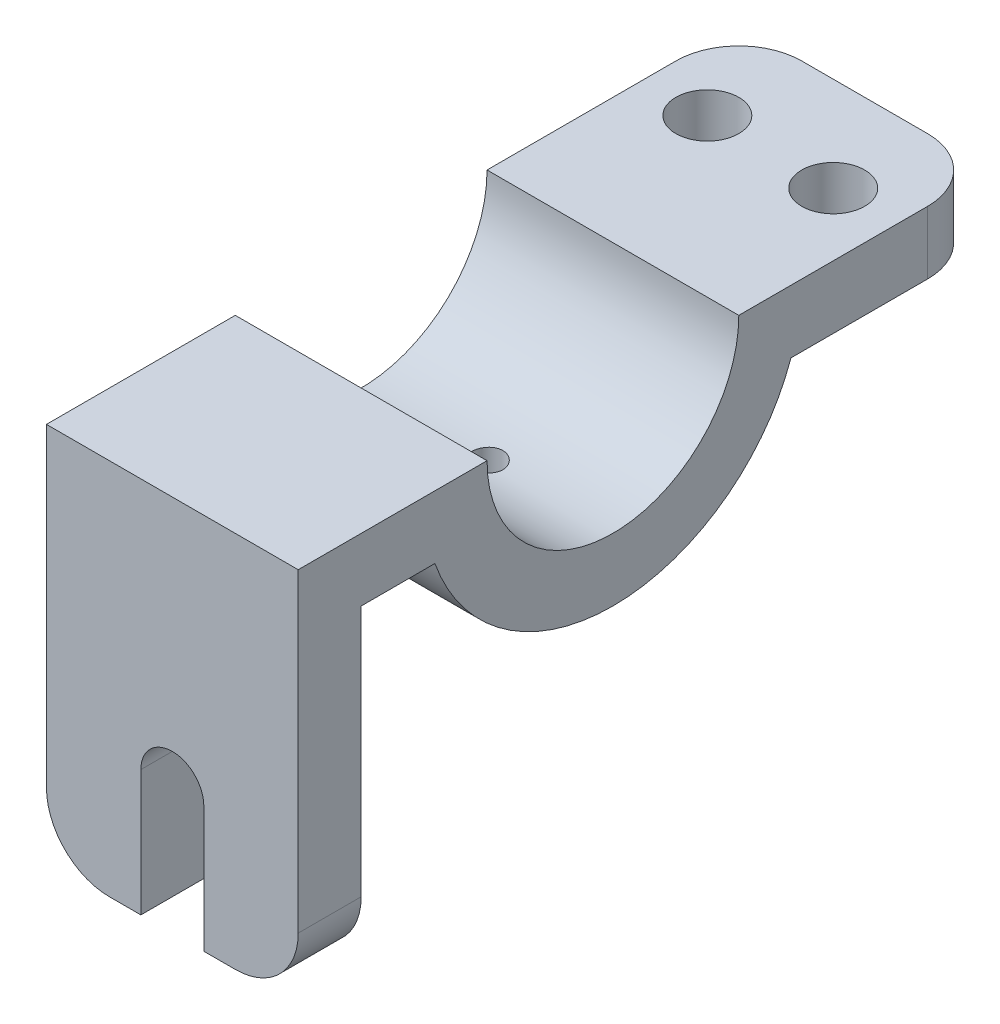
SolidWorks part; units mm, degrees
ref_plane "Front Plane" through (0, 0, 0) normal (0, 0, 1) x (1, 0, 0)
ref_plane "Top Plane" through (0, 0, 0) normal (0, 1, 0) x (1, 0, 0)
ref_plane "Right Plane" through (0, 0, 0) normal (1, 0, 0) x (0, 0, -1)
sketch "Sketch2" plane through (0, 0, 0) normal (1, 0, 0) x (0, 0, -1)
  line L0 (0, 0) -> (38.1, 0)
  line L1 (0, 0) -> (0, -76.2)
  line L2 (0, -76.2) -> (12.7, -76.2)
  line L3 (12.7, -76.2) -> (12.7, -12.7)
  line L4 (12.7, -12.7) -> (27.579, -12.7)
  line L5 (139.7, -12.7) -> (139.7, 0)
  line L6 (88.9, 0) -> (139.7, 0)
  line L7 (99.421, -12.7) -> (139.7, -12.7)
  arc A1 (38.1, 0) -> (88.9, 0) centre (63.5, 0) ccw
  arc A2 (27.579, -12.7) -> (99.421, -12.7) centre (63.5, 0) ccw
  dimension "D5" = 63.5
  dimension "D6" = 50.8
  dimension "D7" = 76.2
  dimension "D1" = 139.7
  dimension "D2" = 76.2
  dimension "D3" = 12.7
  dimension "D4" = 63.5
extrude "Boss-Extrude1" add sketch "Sketch2" along normal blind 50.8
sketch "Sketch3" plane through (0, 0, 0) normal (0, 0, 1) x (1, 0, 0)
  line L5 (50.8, -63.5) -> (50.8, -76.2)
  line L6 (50.8, -76.2) -> (38.1, -76.2)
  arc A0 (38.1, -76.2) -> (50.8, -63.5) centre (38.1, -63.5) ccw
  point P10 (50.8, -76.2)
  dimension "D3" = 12.7
extrude "Cut-Extrude1" cut sketch "Sketch3" against normal blind 22.86
sketch "Sketch4" plane through (0, 0, 0) normal (0, 0, 1) x (1, 0, 0)
  line L1 (0, -63.5) -> (0, -76.2)
  line L3 (0, -76.2) -> (12.7, -76.2)
  arc A0 (0, -63.5) -> (12.7, -76.2) centre (12.7, -63.5) ccw
  point P10 (0, -76.2)
  dimension "D3" = 12.7
extrude "Cut-Extrude2" cut sketch "Sketch4" against normal blind 22.86
sketch "Sketch5" plane through (0, 0, 0) normal (0, 0, 1) x (1, 0, 0)
  line L0 (19.05, -76.2) -> (19.05, -50.8)
  line L1 (38.1, -76.2) -> (12.7, -76.2) construction
  line L3 (31.75, -50.8) -> (31.75, -76.2)
  line L4 (31.75, -76.2) -> (19.05, -76.2)
  arc A0 (31.75, -50.8) -> (19.05, -50.8) centre (25.4, -50.8) ccw
  point P8 (0, 0)
  dimension "D4" = 12.7
  dimension "D1" = 19.05
  dimension "D2" = 12.7
  dimension "D3" = 25.4
extrude "Cut-Extrude3" cut sketch "Sketch5" against normal blind 22.86
sketch "Sketch6" plane through (0, 0, 0) normal (0, 1, 0) x (1, 0, 0)
  line L0 (50.8, 0) -> (0, 0) construction
  line L1 (50.8, 38.1) -> (50.8, 0) construction
  circle A0 centre (25.4, 63.5) radius 3.175
  dimension "D1" = 6.35
  dimension "D3" = 25.4
  dimension "D2" = 63.5
extrude "Cut-Extrude4" cut sketch "Sketch6" against normal blind 60.96
sketch "Sketch7" plane through (0, 0, 0) normal (0, 1, 0) x (1, 0, 0)
  line L5 (0, 127) -> (0, 139.7)
  line L6 (0, 139.7) -> (12.7, 139.7)
  arc A0 (12.7, 139.7) -> (0, 127) centre (12.7, 127) ccw
  point P10 (0, 139.7)
  dimension "D3" = 12.7
extrude "Cut-Extrude5" cut sketch "Sketch7" against normal blind 30.48
ref_plane "Plane1" through (50.8, 0, -139.7) normal (-1, 0, 0) x (0, 0, 1)
sketch "Sketch9" plane through (0, 0, 0) normal (0, 1, 0) x (1, 0, 0)
  line L5 (50.8, 127) -> (50.8, 139.7)
  line L6 (50.8, 139.7) -> (38.1, 139.7)
  arc A0 (38.1, 139.7) -> (50.8, 127) centre (38.1, 127) cw
  point P10 (50.8, 139.7)
  dimension "D3" = 12.7
extrude "Cut-Extrude6" cut sketch "Sketch9" against normal blind 30.48
sketch "Sketch10" plane through (0, 0, 0) normal (0, 1, 0) x (1, 0, 0)
  line L0 (38.1, 139.7) -> (12.7, 139.7) construction
  line L1 (0, 127) -> (0, 88.9) construction
  circle A0 centre (38.1, 120.65) radius 6.35
  circle A1 centre (12.7, 120.65) radius 6.35
  dimension "D1" = 12.7
  dimension "D5" = 12.7
  dimension "D2" = 12.7
  dimension "D3" = 19.05
  dimension "D4" = 2
extrude "Cut-Extrude7" cut sketch "Sketch10" against normal blind 30.48
